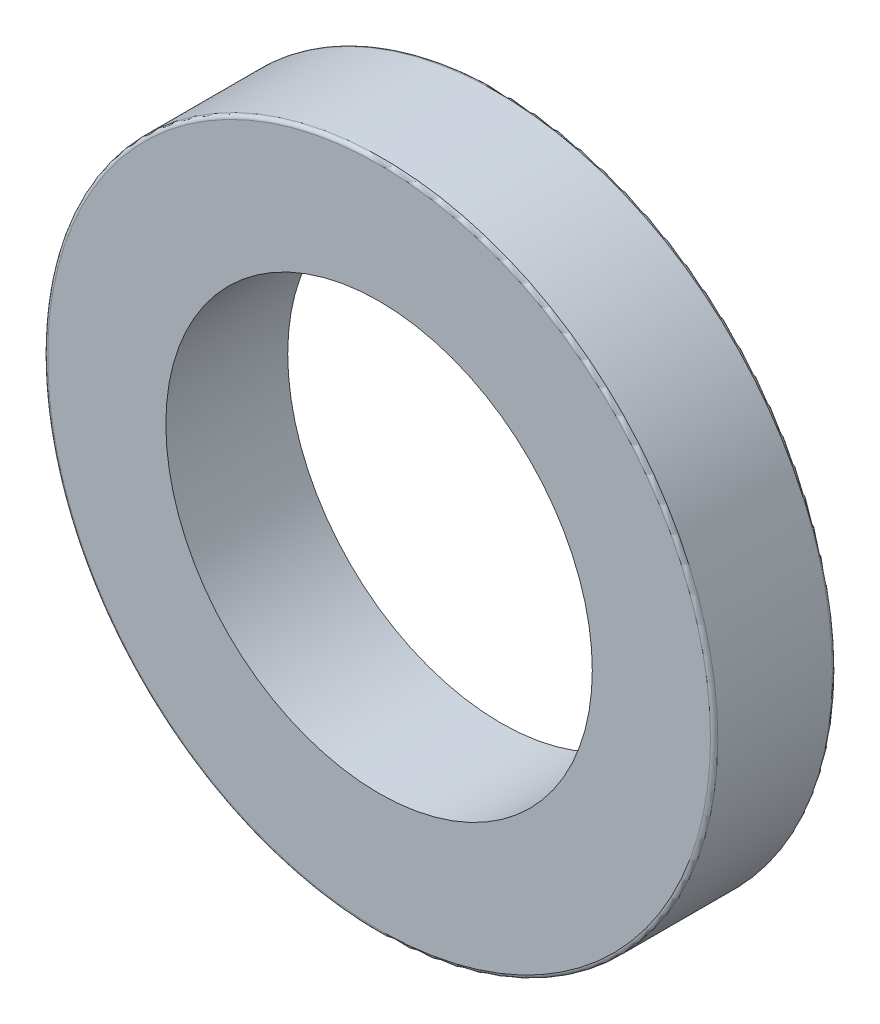
SolidWorks part; units mm, degrees
ref_plane "Front Plane" through (0, 0, 0) normal (0, 0, 1) x (1, 0, 0)
ref_plane "Top Plane" through (0, 0, 0) normal (0, 1, 0) x (1, 0, 0)
ref_plane "Right Plane" through (0, 0, 0) normal (1, 0, 0) x (0, 0, -1)
sketch "Sketch1" plane through (0, 0, 0) normal (0, 0, 1) x (1, 0, 0)
  circle A0 centre (0, 0) radius 27.5
  circle A1 centre (0, 0) radius 17.5
  dimension "D1" = 35
  dimension "D2" = 55
extrude "Boss-Extrude1" add sketch "Sketch1" along normal blind 10
fillet "Fillet1" radius 0.3 2 edges at (27.5, 0, 0) (27.5, 0, 10)
